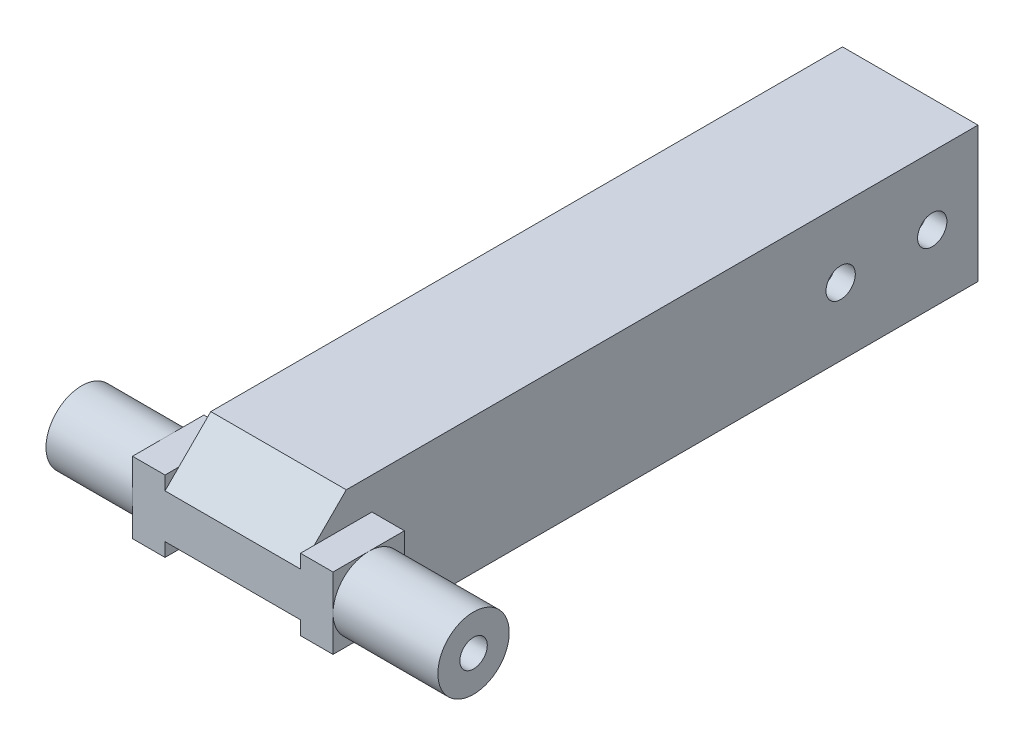
SolidWorks part; units mm, degrees
ref_plane "Спереди" through (0, 0, 0) normal (0, 0, 1) x (1, 0, 0)
ref_plane "Сверху" through (0, 0, 0) normal (0, 1, 0) x (1, 0, 0)
ref_plane "Справа" through (0, 0, 0) normal (1, 0, 0) x (0, 0, -1)
sketch "Эскиз1" plane through (0, 0, 0) normal (1, 0, 0) x (0, 0, -1)
  line L1 (37, -7.4) -> (-37, -7.4)
  line L2 (37, -7.4) -> (37, 7.4)
  line L3 (37, 7.4) -> (-37, 7.4)
  line L4 (-37, -7.4) -> (-37, 7.4)
  line L5 (37, -7.4) -> (-37, 7.4) construction
  line L6 (37, 7.4) -> (-37, -7.4) construction
  point P0 (0, 0)
  dimension "D1" = 14.8
  dimension "D2" = 74
extrude "Бобышка-Вытянуть1" add sketch "Эскиз1" along normal blind 14.8
sketch "Эскиз2" plane through (0, 0, -37) normal (0, 0, -1) x (-1, 0, 0)
  line L0 (0, 7.4) -> (-14.8, -7.4) construction
  line L2 (-2.2, -5.2) -> (-12.6, -5.2)
  line L3 (-2.2, -5.2) -> (-2.2, 5.2)
  line L4 (-2.2, 5.2) -> (-12.6, 5.2)
  line L5 (-12.6, -5.2) -> (-12.6, 5.2)
  line L6 (-2.2, -5.2) -> (-12.6, 5.2) construction
  line L7 (-2.2, 5.2) -> (-12.6, -5.2) construction
  point P4 (-7.4, 0)
  dimension "D1" = 10.4
extrude "Вырез-Вытянуть1" cut sketch "Эскиз2" against normal blind 30
sketch "Эскиз3" plane through (14.8, 0, 0) normal (1, 0, 0) x (0, 0, -1)
  line L0 (37, 0) -> (-37, 0) construction
  line L1 (37, -7.4) -> (37, 7.4) construction
  line L2 (-37, 7.4) -> (-37, -7.4) construction
  circle A0 centre (-33.1, 0) radius 3.9
  dimension "D1" = 7.8
extrude "Бобышка-Вытянуть2" add sketch "Эскиз3" along normal blind 15
sketch "Эскиз4" plane through (0, 0, 0) normal (-1, 0, 0) x (0, 0, 1)
  line L0 (37, 0) -> (-37, 0) construction
  line L1 (37, 7.4) -> (37, -7.4) construction
  line L2 (-37, -7.4) -> (-37, 7.4) construction
  circle A0 centre (33.1, 0) radius 3.9
  dimension "D1" = 7.8
extrude "Бобышка-Вытянуть3" add sketch "Эскиз4" along normal blind 13
chamfer "Фаска1" distance 5 angle 45 2 edges at (7.4, -7.4, 37) (7.4, 7.4, 37)
sketch "Эскиз8" plane through (29.8, 0, 0) normal (1, 0, 0) x (0, 0, -1)
  circle A0 centre (-33.1, 0) radius 1.45
  dimension "D1" = 2.9
extrude "Вырез-Вытянуть4" cut sketch "Эскиз8" against normal through all
sketch "Эскиз9" plane through (0, 0, 0) normal (-1, 0, 0) x (0, 0, 1)
  line L1 (37, -3.9) -> (29.2, -3.9)
  line L2 (37, -3.9) -> (37, 3.9)
  line L3 (37, 3.9) -> (29.2, 3.9)
  line L4 (29.2, -3.9) -> (29.2, 3.9)
  line L5 (37, -3.9) -> (29.2, 3.9) construction
  line L6 (37, 3.9) -> (29.2, -3.9) construction
  circle A0 centre (33.1, 0) radius 3.9 construction
  circle A1 centre (33.1, 0) radius 1.5
  point P0 (33.1, 0)
  point P6 (29.2, 0)
  point P11 (33.1, 3.9)
  dimension "D1" = 3
extrude "Бобышка-Вытянуть4" add sketch "Эскиз9" along normal blind 3.55
sketch "Эскиз10" plane through (14.8, 0, 0) normal (1, 0, 0) x (0, 0, -1)
  line L1 (-37, -3.9) -> (-29.2, -3.9)
  line L2 (-37, -3.9) -> (-37, 3.9)
  line L3 (-37, 3.9) -> (-29.2, 3.9)
  line L4 (-29.2, -3.9) -> (-29.2, 3.9)
  line L5 (-37, -3.9) -> (-29.2, 3.9) construction
  line L6 (-37, 3.9) -> (-29.2, -3.9) construction
  circle A0 centre (-33.1, 0) radius 3.9 construction
  point P0 (-33.1, 0)
  point P6 (-29.2, 0)
  point P9 (-33.1, 3.9)
extrude "Бобышка-Вытянуть5" add sketch "Эскиз10" along normal blind 3.55
sketch "Sketch1" plane through (0, 0, 0) normal (-1, 0, 0) x (0, 0, 1)
  line L0 (-37, 0) -> (29.2, 0) construction
  line L1 (-37, -7.4) -> (-37, 7.4) construction
  line L2 (29.2, 3.9) -> (29.2, -3.9) construction
  circle A0 centre (-32, 0) radius 1.6
  circle A1 centre (-22, 0) radius 1.6
  dimension "D1" = 3.2
  dimension "D2" = 5
  dimension "D3" = 15
extrude "Cut-Extrude1" cut sketch "Sketch1" against normal through all
sketch "Sketch2" plane through (29.8, 0, 0) normal (1, 0, 0) x (0, 0, -1)
  circle A0 centre (-33.1, 0) radius 1.5
extrude "Cut-Extrude2" cut sketch "Sketch2" against normal through all
